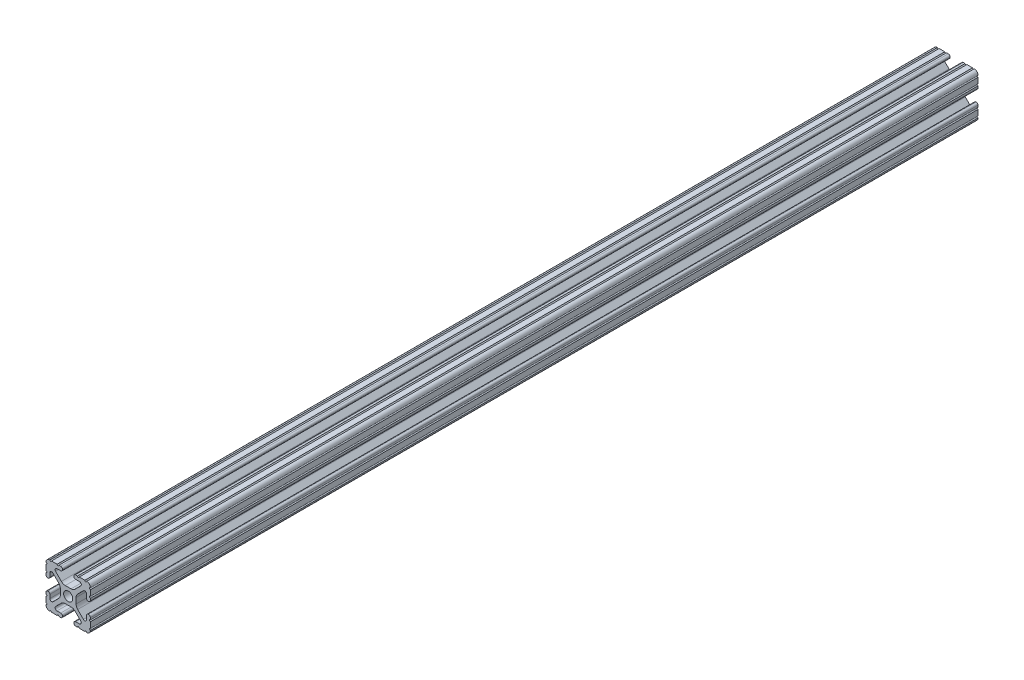
SolidWorks part; units mm, degrees
ref_plane "Front Plane" through (0, 0, 0) normal (0, 0, 1) x (1, 0, 0)
ref_plane "Top Plane" through (0, 0, 0) normal (0, 1, 0) x (1, 0, 0)
ref_plane "Right Plane" through (0, 0, 0) normal (1, 0, 0) x (0, 0, -1)
sketch "Sketch1" plane through (0, 0, 0) normal (0, 0, 1) x (1, 0, 0)
  line L88 (-7.1797, -8.6452) -> (-3.9523, -5.4237)
  line L89 (-1.7093, -4.4958) -> (1.7093, -4.4958)
  line L90 (3.9523, -5.4237) -> (7.1797, -8.6452)
  line L91 (6.4164, -10.4902) -> (4.2875, -10.4902)
  line L92 (3.2385, -11.5392) -> (3.2385, -11.651)
  line L93 (4.2875, -12.7) -> (5.3171, -12.7)
  line L94 (6.3331, -12.7) -> (9.5504, -12.7)
  line L95 (12.7, -9.5504) -> (12.7, -6.3331)
  line L96 (12.7, -5.3171) -> (12.7, -4.2875)
  line L97 (11.651, -3.2385) -> (11.5392, -3.2385)
  line L98 (10.4902, -4.2875) -> (10.4902, -6.4021)
  line L99 (8.7371, -7.1294) -> (5.441, -3.8408)
  line L100 (4.5085, -1.5932) -> (4.5085, 1.5932)
  line L101 (5.441, 3.8408) -> (8.7371, 7.1294)
  line L102 (10.4902, 6.4021) -> (10.4902, 4.2875)
  line L103 (11.5392, 3.2385) -> (11.651, 3.2385)
  line L104 (12.7, 4.2875) -> (12.7, 5.3171)
  line L105 (12.7, 6.3331) -> (12.7, 9.5504)
  line L106 (9.5504, 12.7) -> (6.3331, 12.7)
  line L107 (5.3171, 12.7) -> (4.2875, 12.7)
  line L108 (3.2385, 11.651) -> (3.2385, 11.5392)
  line L109 (4.2875, 10.4902) -> (6.4768, 10.4902)
  line L110 (7.207, 8.7244) -> (3.8983, 5.4232)
  line L111 (1.6558, 4.4958) -> (-1.6558, 4.4958)
  line L112 (-3.8983, 5.4232) -> (-7.207, 8.7244)
  line L113 (-6.4768, 10.4902) -> (-4.2875, 10.4902)
  line L114 (-3.2385, 11.5392) -> (-3.2385, 11.651)
  line L115 (-4.2875, 12.7) -> (-5.3171, 12.7)
  line L116 (-6.3331, 12.7) -> (-9.5504, 12.7)
  line L117 (-12.7, 9.5504) -> (-12.7, 6.3331)
  line L118 (-12.7, 5.3171) -> (-12.7, 4.2875)
  line L119 (-11.651, 3.2385) -> (-11.5392, 3.2385)
  line L120 (-10.4902, 4.2875) -> (-10.4902, 6.4021)
  line L121 (-8.7371, 7.1294) -> (-5.441, 3.8408)
  line L122 (-4.5085, 1.5932) -> (-4.5085, -1.5932)
  line L123 (-5.441, -3.8408) -> (-8.7371, -7.1294)
  line L124 (-10.4902, -6.4021) -> (-10.4902, -4.2875)
  line L125 (-11.5392, -3.2385) -> (-11.651, -3.2385)
  line L126 (-12.7, -4.2875) -> (-12.7, -5.3171)
  line L127 (-12.7, -6.3331) -> (-12.7, -9.5504)
  line L128 (-9.5504, -12.7) -> (-6.3331, -12.7)
  line L129 (-5.3171, -12.7) -> (-4.2875, -12.7)
  line L130 (-3.2385, -11.651) -> (-3.2385, -11.5392)
  line L131 (-4.2875, -10.4902) -> (-6.4164, -10.4902)
  circle A1 centre (0, 0) radius 2.6035
  arc A104 (-7.1797, -8.6452) -> (-6.4164, -10.4902) centre (-6.4164, -9.4098) ccw
  arc A105 (-1.7093, -4.4958) -> (-3.9523, -5.4237) centre (-1.7093, -7.6708) ccw
  arc A106 (3.9523, -5.4237) -> (1.7093, -4.4958) centre (1.7093, -7.6708) ccw
  arc A107 (6.4164, -10.4902) -> (7.1797, -8.6452) centre (6.4164, -9.4098) ccw
  arc A108 (4.2875, -10.4902) -> (3.2385, -11.5392) centre (4.2875, -11.5392) ccw
  arc A109 (3.2385, -11.651) -> (4.2875, -12.7) centre (4.2875, -11.651) ccw
  arc A110 (6.3331, -12.7) -> (5.3171, -12.7) centre (5.8251, -12.7) ccw
  arc A111 (10.5664, -12.6998) -> (9.5504, -12.7) centre (10.0584, -12.7) ccw
  arc A112 (10.5664, -12.6998) -> (12.6998, -10.5664) centre (10.5918, -10.5918) ccw
  arc A113 (12.7, -9.5504) -> (12.6998, -10.5664) centre (12.7, -10.0584) ccw
  arc A114 (12.7, -5.3171) -> (12.7, -6.3331) centre (12.7, -5.8251) ccw
  arc A115 (12.7, -4.2875) -> (11.651, -3.2385) centre (11.651, -4.2875) ccw
  arc A116 (11.5392, -3.2385) -> (10.4902, -4.2875) centre (11.5392, -4.2875) ccw
  arc A117 (8.7371, -7.1294) -> (10.4902, -6.4021) centre (9.4628, -6.4021) ccw
  arc A118 (4.5085, -1.5932) -> (5.441, -3.8408) centre (7.6835, -1.5932) ccw
  arc A119 (5.441, 3.8408) -> (4.5085, 1.5932) centre (7.6835, 1.5932) ccw
  arc A120 (10.4902, 6.4021) -> (8.7371, 7.1294) centre (9.4628, 6.4021) ccw
  arc A121 (10.4902, 4.2875) -> (11.5392, 3.2385) centre (11.5392, 4.2875) ccw
  arc A122 (11.651, 3.2385) -> (12.7, 4.2875) centre (11.651, 4.2875) ccw
  arc A123 (12.7, 6.3331) -> (12.7, 5.3171) centre (12.7, 5.8251) ccw
  arc A124 (12.6998, 10.5664) -> (12.7, 9.5504) centre (12.7, 10.0584) ccw
  arc A125 (12.6998, 10.5664) -> (10.5664, 12.6998) centre (10.5918, 10.5918) ccw
  arc A126 (9.5504, 12.7) -> (10.5664, 12.6998) centre (10.0584, 12.7) ccw
  arc A127 (5.3171, 12.7) -> (6.3331, 12.7) centre (5.8251, 12.7) ccw
  arc A128 (4.2875, 12.7) -> (3.2385, 11.651) centre (4.2875, 11.651) ccw
  arc A129 (3.2385, 11.5392) -> (4.2875, 10.4902) centre (4.2875, 11.5392) ccw
  arc A130 (7.207, 8.7244) -> (6.4768, 10.4902) centre (6.4768, 9.4563) ccw
  arc A131 (1.6558, 4.4958) -> (3.8983, 5.4232) centre (1.6558, 7.6708) ccw
  arc A132 (-3.8983, 5.4232) -> (-1.6558, 4.4958) centre (-1.6558, 7.6708) ccw
  arc A133 (-6.4768, 10.4902) -> (-7.207, 8.7244) centre (-6.4768, 9.4563) ccw
  arc A134 (-4.2875, 10.4902) -> (-3.2385, 11.5392) centre (-4.2875, 11.5392) ccw
  arc A135 (-3.2385, 11.651) -> (-4.2875, 12.7) centre (-4.2875, 11.651) ccw
  arc A136 (-6.3331, 12.7) -> (-5.3171, 12.7) centre (-5.8251, 12.7) ccw
  arc A137 (-10.5664, 12.6998) -> (-9.5504, 12.7) centre (-10.0584, 12.7) ccw
  arc A138 (-10.5664, 12.6998) -> (-12.6998, 10.5664) centre (-10.5918, 10.5918) ccw
  arc A139 (-12.7, 9.5504) -> (-12.6998, 10.5664) centre (-12.7, 10.0584) ccw
  arc A140 (-12.7, 5.3171) -> (-12.7, 6.3331) centre (-12.7, 5.8251) ccw
  arc A141 (-12.7, 4.2875) -> (-11.651, 3.2385) centre (-11.651, 4.2875) ccw
  arc A142 (-11.5392, 3.2385) -> (-10.4902, 4.2875) centre (-11.5392, 4.2875) ccw
  arc A143 (-8.7371, 7.1294) -> (-10.4902, 6.4021) centre (-9.4628, 6.4021) ccw
  arc A144 (-4.5085, 1.5932) -> (-5.441, 3.8408) centre (-7.6835, 1.5932) ccw
  arc A145 (-5.441, -3.8408) -> (-4.5085, -1.5932) centre (-7.6835, -1.5932) ccw
  arc A146 (-10.4902, -6.4021) -> (-8.7371, -7.1294) centre (-9.4628, -6.4021) ccw
  arc A147 (-10.4902, -4.2875) -> (-11.5392, -3.2385) centre (-11.5392, -4.2875) ccw
  arc A148 (-11.651, -3.2385) -> (-12.7, -4.2875) centre (-11.651, -4.2875) ccw
  arc A149 (-12.7, -6.3331) -> (-12.7, -5.3171) centre (-12.7, -5.8251) ccw
  arc A150 (-12.6998, -10.5664) -> (-12.7, -9.5504) centre (-12.7, -10.0584) ccw
  arc A151 (-12.6998, -10.5664) -> (-10.5664, -12.6998) centre (-10.5918, -10.5918) ccw
  arc A152 (-9.5504, -12.7) -> (-10.5664, -12.6998) centre (-10.0584, -12.7) ccw
  arc A153 (-5.3171, -12.7) -> (-6.3331, -12.7) centre (-5.8251, -12.7) ccw
  arc A154 (-4.2875, -12.7) -> (-3.2385, -11.651) centre (-4.2875, -11.651) ccw
  arc A155 (-3.2385, -11.5392) -> (-4.2875, -10.4902) centre (-4.2875, -11.5392) ccw
extrude "Boss-Extrude1" add sketch "Sketch1" along normal mid plane 508
